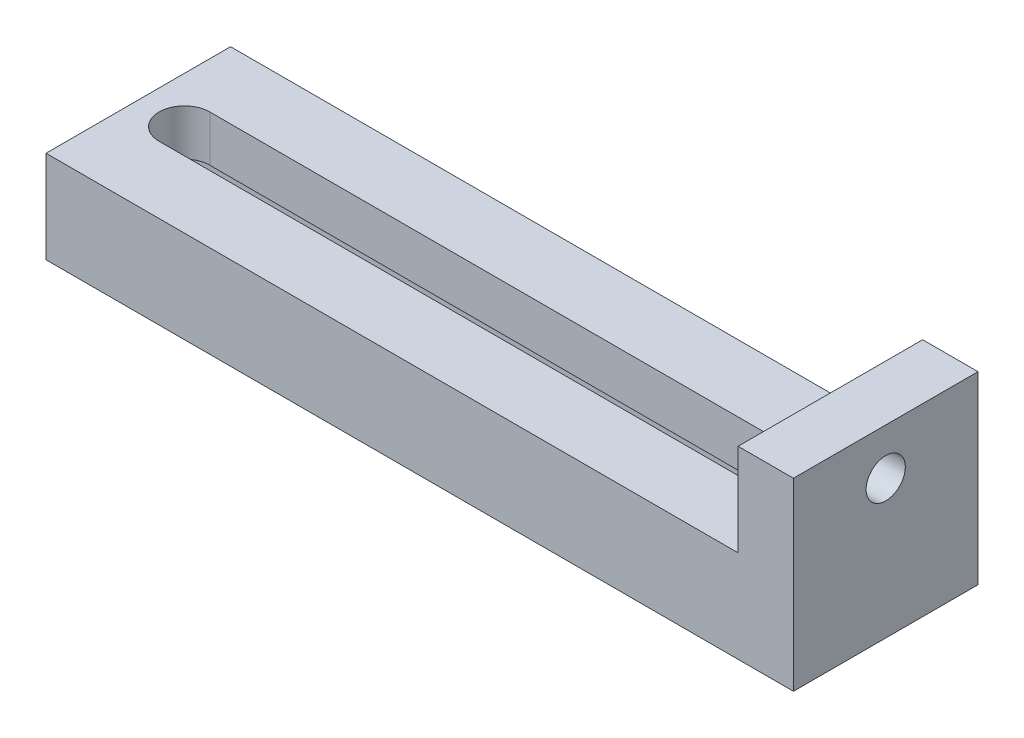
SolidWorks part; units mm, degrees
ref_plane "前视基准面" through (0, 0, 0) normal (0, 0, 1) x (1, 0, 0)
ref_plane "上视基准面" through (0, 0, 0) normal (0, 1, 0) x (1, 0, 0)
ref_plane "右视基准面" through (0, 0, 0) normal (1, 0, 0) x (0, 0, -1)
sketch "草图1" plane through (0, 0, 0) normal (0, 1, 0) x (1, 0, 0)
  line L1 (-75, 20) -> (75, 20)
  line L2 (-75, 20) -> (-75, -20)
  line L3 (-75, -20) -> (75, -20)
  line L4 (75, 20) -> (75, -20)
  line L5 (-75, 20) -> (75, -20) construction
  line L6 (-75, -20) -> (75, 20) construction
  point P0 (0, 0)
  dimension "D1" = 150
  dimension "D2" = 40
extrude "凸台-拉伸1" add sketch "草图1" along normal blind 20
sketch "草图2" plane through (0, 20, 0) normal (0, 1, 0) x (1, 0, 0)
  line L0 (47.5, 0) -> (-47.5, 0) construction
  line L1 (-1662.5, 0) -> (37.5, 0) construction
  line L2 (0, 36.4384) -> (0, -29.528) construction
  dimension "D1" = 95
sketch "草图3" plane through (0, 0, 0) normal (0, -1, 0) x (1, 0, 0)
  line L0 (75, -20) -> (-75, -20) construction
  line L1 (75, 20) -> (87, 20)
  line L2 (75, 20) -> (75, -20)
  line L3 (75, -20) -> (87, -20)
  line L4 (87, 20) -> (87, -20)
  dimension "D1" = 12
extrude "凸台-拉伸2" add sketch "草图3" against normal blind 40
sketch "草图4" plane through (0, 20, 0) normal (0, 1, 0) x (1, 0, 0)
  line L0 (-65, 0) -> (65, 0) construction
  line L1 (47.5, 0) -> (-47.5, 0) construction
  line L2 (-65, 5.5) -> (65, 5.5)
  line L3 (-65, -5.5) -> (65, -5.5)
  line L4 (-75, 20) -> (-75, -20) construction
  line L5 (0, 36.4384) -> (0, -29.528) construction
  line L6 (0, 36.4384) -> (0, -29.528) construction
  line L7 (75, -20) -> (75, 20) construction
  arc A0 (-65, 5.5) -> (-65, -5.5) centre (-65, 0) ccw
  arc A1 (65, -5.5) -> (65, 5.5) centre (65, 0) ccw
  point P4 (0, 0)
  dimension "D1" = 11
  dimension "D2" = 10
  dimension "D3" = 10
extrude "切除-拉伸1" cut sketch "草图4" against normal blind 40 contours L3 A1 L2 A0
hole_wizard "M10 螺纹孔1" positions "草图5" profile "草图6" tap size "M10" standard "GB"
sketch "草图5" plane through (87, 0, 0) normal (1, 0, 0) x (0, 0, -1)
  line L0 (-20, 40) -> (-20, 0) construction
  line L1 (20, 40) -> (-20, 40) construction
  point P0 (0, 30)
  dimension "D1" = 20
  dimension "D2" = 10
sketch "草图6" plane through (87, 30, 0) normal (0, 1, 0) x (0, 0, -1)
  line L0 (0, 0) -> (0, 27.0537)
  line L1 (0, 27.0537) -> (4.25, 24.5)
  line L2 (4.25, 24.5) -> (4.25, 0)
  line L5 (4.25, 0) -> (0, 0)
  line L10 (0, 27.0537) -> (-4.25, 24.5) construction
  line L11 (0, -6.35) -> (0, 107.95) construction
  dimension "螺纹孔钻头直径" = 8.5
  dimension "螺纹孔钻头深度" = 24.5
  dimension "导头角度" = 118
cosmetic thread "孔螺蚊线1" parameters "D1"=20, "D2"=10
sketch "草图7" plane through (-75, 0, 0) normal (-1, 0, 0) x (0, 0, 1)
  line L0 (-20, 0) -> (20, 0) construction
  line L1 (-8, 0) -> (8, 0)
  line L2 (-8, 0) -> (-8, 10)
  line L3 (-8, 10) -> (8, 10)
  line L4 (8, 0) -> (8, 10)
  line L5 (-20, 20) -> (20, 20) construction
  point P6 (0, 10)
  point P9 (0, 20)
  dimension "D1" = 16
  dimension "D2" = 10
  dimension "D3" = 0
extrude "切除-拉伸2" cut sketch "草图7" against normal up to surface (150 mm away) up to face at (75, 30, 4.25)
